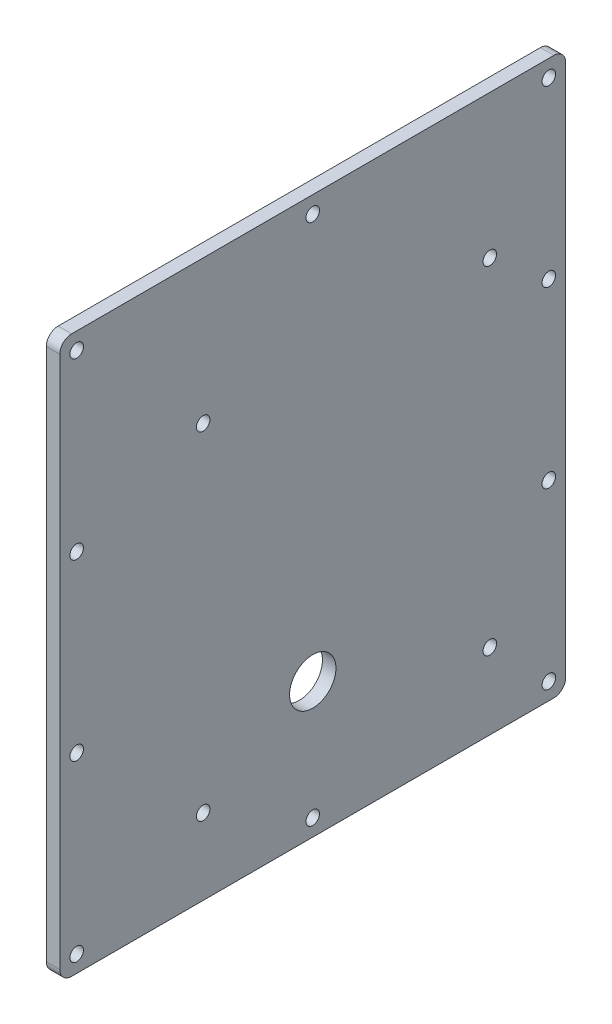
SolidWorks part; units mm, degrees
material "Acrylic (Medium-high impact)"
ref_plane "Front Plane" through (0, 0, 0) normal (0, 0, 1) x (1, 0, 0)
ref_plane "Top Plane" through (0, 0, 0) normal (0, 1, 0) x (1, 0, 0)
ref_plane "Right Plane" through (0, 0, 0) normal (1, 0, 0) x (0, 0, -1)
sketch "Sketch1" plane through (0, 0, 0) normal (1, 0, 0) x (0, 0, -1)
  line L1 (0, 0) -> (190.5, 0)
  line L2 (0, 0) -> (0, 209.55)
  line L3 (0, 209.55) -> (190.5, 209.55)
  line L4 (190.5, 0) -> (190.5, 209.55)
  dimension "D1" = 190.5
  dimension "D2" = 209.55
extrude "Boss-Extrude2" add sketch "Sketch1" along normal blind 5.08
sketch "Sketch2" plane through (5.08, 0, 0) normal (1, 0, 0) x (0, 0, -1)
  line L0 (0, 0) -> (190.5, 0) construction
  circle A3 centre (95.25, 50.8) radius 8.7313
  point P5 (95.25, 0)
  dimension "D1" = 50.8
  dimension "D2" = 17.4625
extrude "Cut-Extrude1" cut sketch "Sketch2" against normal through all
hole_wizard "#10 Clearance Hole2" positions "Sketch5" profile "Sketch6" hole size "#10" standard "ANSI Inch" end condition through all
sketch "Sketch5" plane through (5.08, 0, 0) normal (1, 0, 0) x (0, 0, -1)
  circle A0 centre (53.975, 28.575) radius 2.5527 construction
  circle A1 centre (161.925, 28.575) radius 2.5527 construction
  circle A2 centre (161.925, 155.575) radius 2.5527 construction
  circle A3 centre (53.975, 155.575) radius 2.5527 construction
  circle A4 centre (53.975, 28.575) radius 2.5527
  circle A5 centre (161.925, 28.575) radius 2.5527
  circle A6 centre (161.925, 155.575) radius 2.5527
  circle A7 centre (53.975, 155.575) radius 2.5527
  point P213 (53.975, 155.575)
  point P216 (161.925, 155.575)
  point P219 (161.925, 28.575)
  point P222 (53.975, 28.575)
sketch "Sketch6" plane through (5.08, 28.575, -53.975) normal (0, 1, 0) x (0, 0, -1)
  line L0 (0, 0) -> (0, 5.08)
  line L1 (0, 5.08) -> (2.5527, 5.08)
  line L2 (2.5527, 5.08) -> (2.5527, 0)
  line L5 (2.5527, 0) -> (0, 0)
  line L11 (0, -6.35) -> (0, 107.95) construction
  dimension "Thru Hole Dia." = 5.1054
  dimension "Thru Hole Depth" = 5.08
fillet "Fillet1" radius 4.445 4 edges at (2.54, 0, 0) (2.54, 0, -190.5) (2.54, 209.55, -190.5) (2.54, 209.55, 0)
hole_wizard "#10 Clearance Hole1" positions "Sketch7" profile "Sketch8" hole size "#10" standard "ANSI Inch" end condition through all
sketch "Sketch7" plane through (5.08, 0, 0) normal (1, 0, 0) x (0, 0, -1)
  line L1 (6.35, 203.2) -> (184.15, 203.2)
  line L2 (6.35, 203.2) -> (6.35, 6.35)
  line L3 (6.35, 6.35) -> (184.15, 6.35)
  line L4 (184.15, 203.2) -> (184.15, 6.35)
  line L5 (6.35, 71.9667) -> (184.15, 71.9667) construction
  line L6 (6.35, 137.5833) -> (184.15, 137.5833) construction
  line L10 (95.25, 203.2) -> (95.25, 137.5833) construction
  line L11 (95.25, 137.5833) -> (95.25, 71.9667) construction
  line L12 (95.25, 71.9667) -> (95.25, 6.35) construction
  line L14 (186.055, 209.55) -> (4.445, 209.55) construction
  line L15 (4.445, 0) -> (186.055, 0) construction
  line L16 (0, 205.105) -> (0, 4.445) construction
  line L17 (190.5, 4.445) -> (190.5, 205.105) construction
  point P1 (6.35, 203.2)
  point P2 (184.15, 6.35)
  point P157 (6.35, 6.35)
  point P158 (184.15, 203.2)
  point P168 (95.25, 6.35)
  point P170 (95.25, 203.2)
  point P172 (6.35, 137.5833)
  point P174 (6.35, 71.9667)
  point P176 (184.15, 71.9667)
  point P179 (184.15, 137.5833)
  dimension "D1" = 6.35
  dimension "D2" = 6.35
  dimension "D3" = 6.35
  dimension "D4" = 6.35
sketch "Sketch8" plane through (5.08, 203.2, -6.35) normal (0, 1, 0) x (0, 0, -1)
  line L0 (0, 0) -> (0, 5.08)
  line L1 (0, 5.08) -> (2.5527, 5.08)
  line L2 (2.5527, 5.08) -> (2.5527, 0)
  line L5 (2.5527, 0) -> (0, 0)
  line L11 (0, -6.35) -> (0, 107.95) construction
  dimension "Thru Hole Dia." = 5.1054
  dimension "Thru Hole Depth" = 5.08
